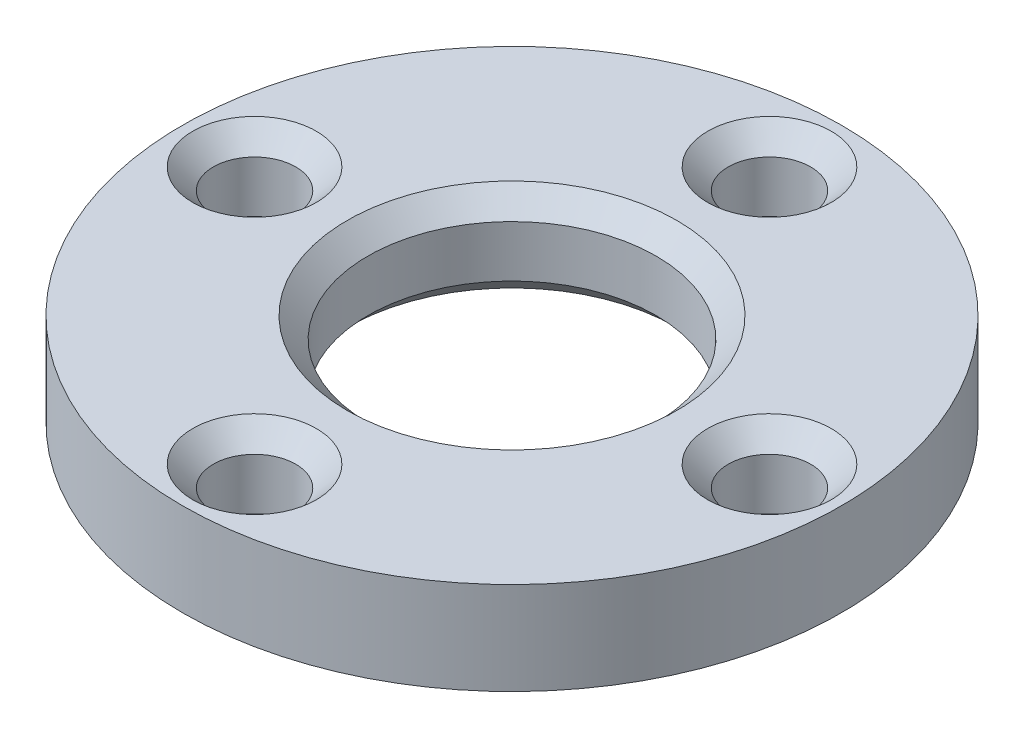
SolidWorks part; units mm, degrees
ref_plane "Front Plane" through (0, 0, 0) normal (0, 0, 1) x (1, 0, 0)
ref_plane "Top Plane" through (0, 0, 0) normal (0, 1, 0) x (1, 0, 0)
ref_plane "Right Plane" through (0, 0, 0) normal (1, 0, 0) x (0, 0, -1)
sketch "Sketch1" plane through (0, 0, 0) normal (0, 1, 0) x (1, 0, 0)
  circle A0 centre (0, 0) radius 16
  circle A1 centre (0, 0) radius 7
  circle A2 centre (0, 0) radius 12.5 construction
  circle A3 centre (0, 12.5) radius 2
  circle A4 centre (12.5, 0) radius 2
  circle A5 centre (0, -12.5) radius 2
  circle A6 centre (-12.5, 0) radius 2
  point P16 (0, 0)
  dimension "D1" = 32
  dimension "D2" = 14
  dimension "D3" = 4
  dimension "D5" = 25
  dimension "D4" = 4
extrude "Boss-Extrude1" add sketch "Sketch1" along normal blind 4.5
chamfer "Chamfer1" distance 1 angle 45 10 edges at (0, 0, 7) (-12.5, 0, 2) (0, 0, -10.5) (12.5, 0, 2) (0, 0, 14.5) (12.5, 4.5, 2) (0, 4.5, -10.5) (-12.5, 4.5, 2) (0, 4.5, 14.5) (0, 4.5, 7)
